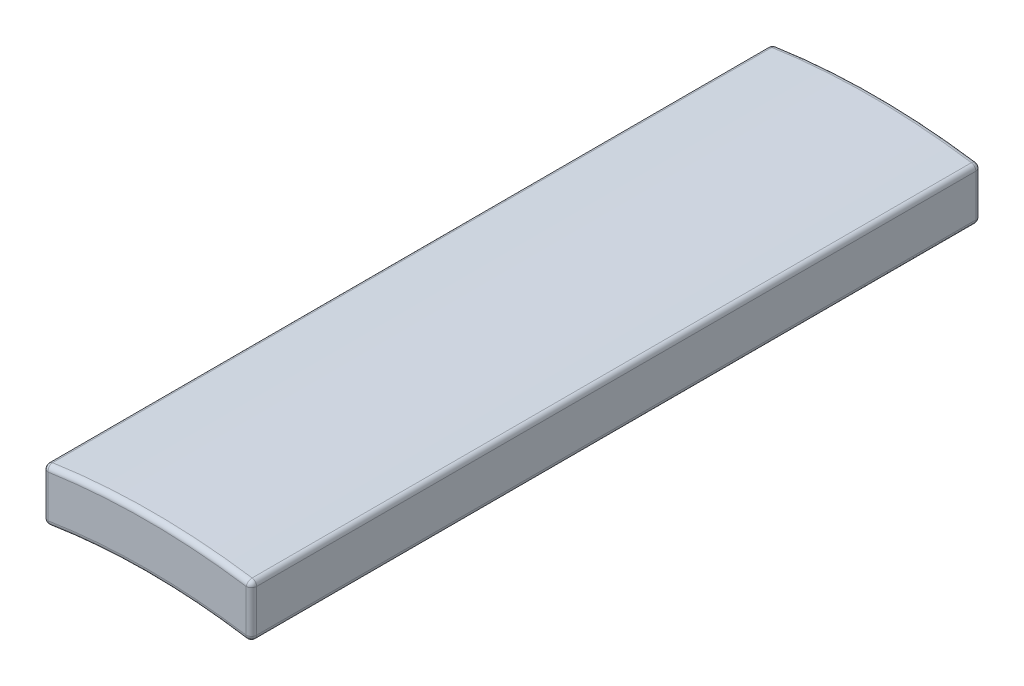
SolidWorks part; units mm, degrees
material "Vanadium"
ref_plane "Front Plane" through (0, 0, 0) normal (0, 0, 1) x (1, 0, 0)
ref_plane "Top Plane" through (0, 0, 0) normal (0, 1, 0) x (1, 0, 0)
ref_plane "Right Plane" through (0, 0, 0) normal (1, 0, 0) x (0, 0, -1)
sketch "Sketch1" plane through (0, 0, 0) normal (0, 0, 1) x (1, 0, 0)
  line L0 (2, 11.8322) -> (2, 12.8452)
  line L7 (-2, 11.8322) -> (-2, 12.8452)
  arc A2 (2, 11.8322) -> (-2, 11.8322) centre (0, 0) ccw
  arc A3 (2, 12.8452) -> (-2, 12.8452) centre (0, 0) ccw
extrude "Boss-Extrude1" add sketch "Sketch1" along normal blind 14
fillet "Fillet1" radius 0.1 12 edges at (2, 12.3387, 14) (-2, 12.3387, 14) (-2, 12.3387, 0) (2, 12.3387, 0) (0, 13, 0) (0, 12, 0) (0, 13, 14) (0, 12, 14) (2, 12.8452, 7) (2, 11.8322, 7) (-2, 12.8452, 7) (-2, 11.8322, 7)
